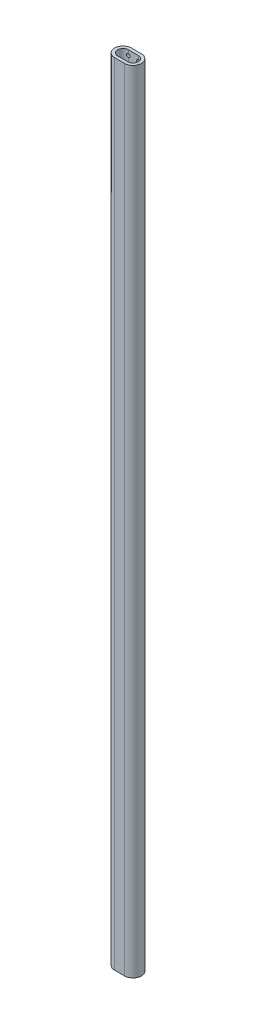
SolidWorks part; units mm, degrees
ref_plane "Front Plane" through (0, 0, 0) normal (0, 0, 1) x (1, 0, 0)
ref_plane "Top Plane" through (0, 0, 0) normal (0, 1, 0) x (1, 0, 0)
ref_plane "Right Plane" through (0, 0, 0) normal (1, 0, 0) x (0, 0, -1)
sketch "Sketch1" plane through (0, 0, 0) normal (0, 1, 0) x (1, 0, 0)
  line L0 (0, 0) -> (38.1, 0) construction
  line L1 (0, 31.75) -> (38.1, 31.75)
  line L2 (0, -31.75) -> (38.1, -31.75)
  line L3 (0, 0) -> (38.1, 0) construction
  line L4 (0, 20.3048) -> (38.1, 20.3048)
  line L5 (0, -20.3048) -> (38.1, -20.3048)
  arc A0 (0, 31.75) -> (0, -31.75) centre (0, 0) ccw
  arc A1 (38.1, -31.75) -> (38.1, 31.75) centre (38.1, 0) ccw
  arc A2 (0, 20.3048) -> (0, -20.3048) centre (0, 0) ccw
  arc A3 (38.1, -20.3048) -> (38.1, 20.3048) centre (38.1, 0) ccw
  point P3 (19.05, 0)
  point P10 (19.05, 0)
  dimension "D1" = 38.1
  dimension "D2" = 63.5
extrude "Boss-Extrude1" add sketch "Sketch1" along normal blind 2997.2
sketch "Sketch2" plane through (0, 0, -31.75) normal (0, 0, -1) x (-1, 0, 0)
  line L0 (-38.1, 0) -> (-38.1, 19.05)
  line L1 (-38.1, 2997.2) -> (-38.1, 0) construction
  line L2 (-19.05, 0) -> (-19.05, 38.1) construction
  line L3 (-38.1, 0) -> (0, 0) construction
  line L4 (-38.1, 2997.2) -> (-38.1, 2978.15)
  line L5 (-19.05, 2997.2) -> (-19.05, 2959.1) construction
  line L6 (-38.1, 2997.2) -> (0, 2997.2) construction
  circle A0 centre (-38.1, 19.05) radius 6.35
  circle A1 centre (0, 19.05) radius 6.35
  circle A2 centre (-38.1, 2978.15) radius 6.35
  circle A3 centre (0, 2978.15) radius 6.35
  dimension "D2" = 12.7
  dimension "D5" = 12.7
  dimension "D1" = 19.05
  dimension "D3" = 38.1
  dimension "D4" = 19.05
  dimension "D6" = 38.1
extrude "Cut-Extrude1" cut sketch "Sketch2" against normal blind 25.4 contours A0 | A1 | A2 | A3
